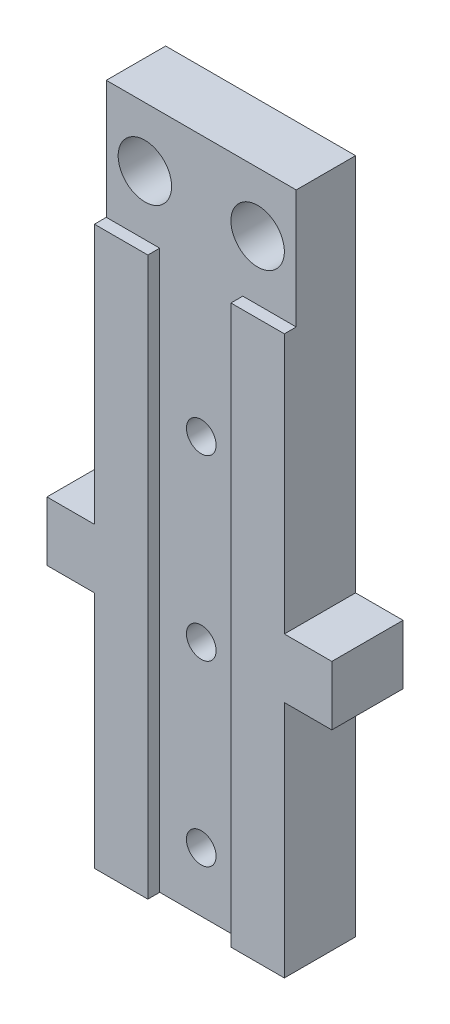
SolidWorks part; units mm, degrees
ref_plane "前视基准面" through (0, 0, 0) normal (0, 0, 1) x (1, 0, 0)
ref_plane "上视基准面" through (0, 0, 0) normal (0, 1, 0) x (1, 0, 0)
ref_plane "右视基准面" through (0, 0, 0) normal (1, 0, 0) x (0, 0, -1)
sketch "草图1" plane through (0, 0, 0) normal (0, 0, 1) x (1, 0, 0)
  line L1 (0, 0) -> (16, 0)
  line L2 (0, 0) -> (0, 57)
  line L3 (0, 57) -> (16, 57)
  line L4 (16, 0) -> (16, 57)
  dimension "D1" = 57
  dimension "D2" = 16
extrude "凸台-拉伸1" add sketch "草图1" along normal blind 6
sketch "草图2" plane through (0, 0, 6) normal (0, 0, 1) x (1, 0, 0)
  line L1 (0, 57) -> (31.7209, 57)
  line L2 (0, 57) -> (0, 47)
  line L3 (0, 47) -> (31.7209, 47)
  line L4 (31.7209, 57) -> (31.7209, 47)
  dimension "D1" = 10
extrude "切除-拉伸1" cut sketch "草图2" against normal blind 1
sketch "草图3" plane through (0, 0, 0) normal (0, 0, -1) x (-1, 0, 0)
  line L0 (-16, 0) -> (-16, 57) construction
  line L1 (-16, 25.1) -> (-20, 25.1)
  line L2 (-16, 25.1) -> (-16, 20.1)
  line L3 (-16, 20.1) -> (-20, 20.1)
  line L4 (-20, 25.1) -> (-20, 20.1)
  line L5 (-8, 57) -> (-8, 0) construction
  line L6 (-16, 57) -> (0, 57) construction
  line L7 (0, 0) -> (-16, 0) construction
  line L8 (0, 25.1) -> (0, 20.1)
  line L9 (0, 20.1) -> (4, 20.1)
  line L10 (4, 25.1) -> (4, 20.1)
  line L11 (0, 25.1) -> (4, 25.1)
  dimension "D1" = 31.9
  dimension "D2" = 5
  dimension "D3" = 24
extrude "凸台-拉伸2" add sketch "草图3" against normal blind 6
hole_wizard "M3 螺纹孔1" positions "草图4" profile "草图5" tap size "M3" standard "ISO"
sketch "草图4" plane through (0, 0, 0) normal (0, 0, -1) x (-1, 0, 0)
  line L0 (-16, 57) -> (0, 57) construction
  line L1 (-8, 57) -> (-8, 30.2909) construction
  point P0 (-8, 35)
  point P2 (-8, 20)
  point P4 (-8, 5)
  point P10 (-8, 57)
  point P15 (0, 0)
  dimension "D1" = 22
  dimension "D2" = 37
  dimension "D3" = 52
sketch "草图5" plane through (8, 35, 0) normal (1, 0, 0) x (0, 1, 0)
  line L0 (0, 0) -> (0, 8.2511)
  line L1 (0, 8.2511) -> (1.25, 7.5)
  line L2 (1.25, 7.5) -> (1.25, 0)
  line L5 (1.25, 0) -> (0, 0)
  line L10 (0, 8.2511) -> (-1.25, 7.5) construction
  line L11 (0, -6.35) -> (0, 107.95) construction
  dimension "螺纹孔钻头直径" = 2.5
  dimension "螺纹孔钻头深度" = 7.5
  dimension "导头角度" = 118
cosmetic thread "孔螺蚊线1" parameters "D1"=6, "D2"=3
cosmetic thread "孔螺蚊线2" parameters "D1"=6, "D2"=3
cosmetic thread "孔螺蚊线3" parameters "D1"=6, "D2"=3
sketch "草图6" plane through (0, 0, 0) normal (0, -1, 0) x (1, 0, 0)
  line L0 (8, 6) -> (8, -12.1397) construction
  line L1 (0, 6) -> (16, 6) construction
  line L3 (11.5, 6) -> (4.5, 6)
  line L4 (11.5, 6) -> (11.5, 5)
  line L5 (11.5, 5) -> (4.5, 5)
  line L6 (4.5, 6) -> (4.5, 5)
  dimension "D1" = 7
  dimension "D2" = 1
extrude "切除-拉伸2" cut sketch "草图6" against normal through all
sketch "草图7" plane through (0, 0, 5) normal (0, 0, 1) x (1, 0, 0)
  line L0 (8, 57) -> (8, 42.3719) construction
  line L1 (16, 57) -> (0, 57) construction
  circle A0 centre (3.25, 52) radius 2.25
  circle A1 centre (12.75, 52) radius 2.25
  dimension "D1" = 9.5
  dimension "D3" = 4.5
  dimension "D2" = 5
extrude "切除-拉伸3" cut sketch "草图7" against normal through all
